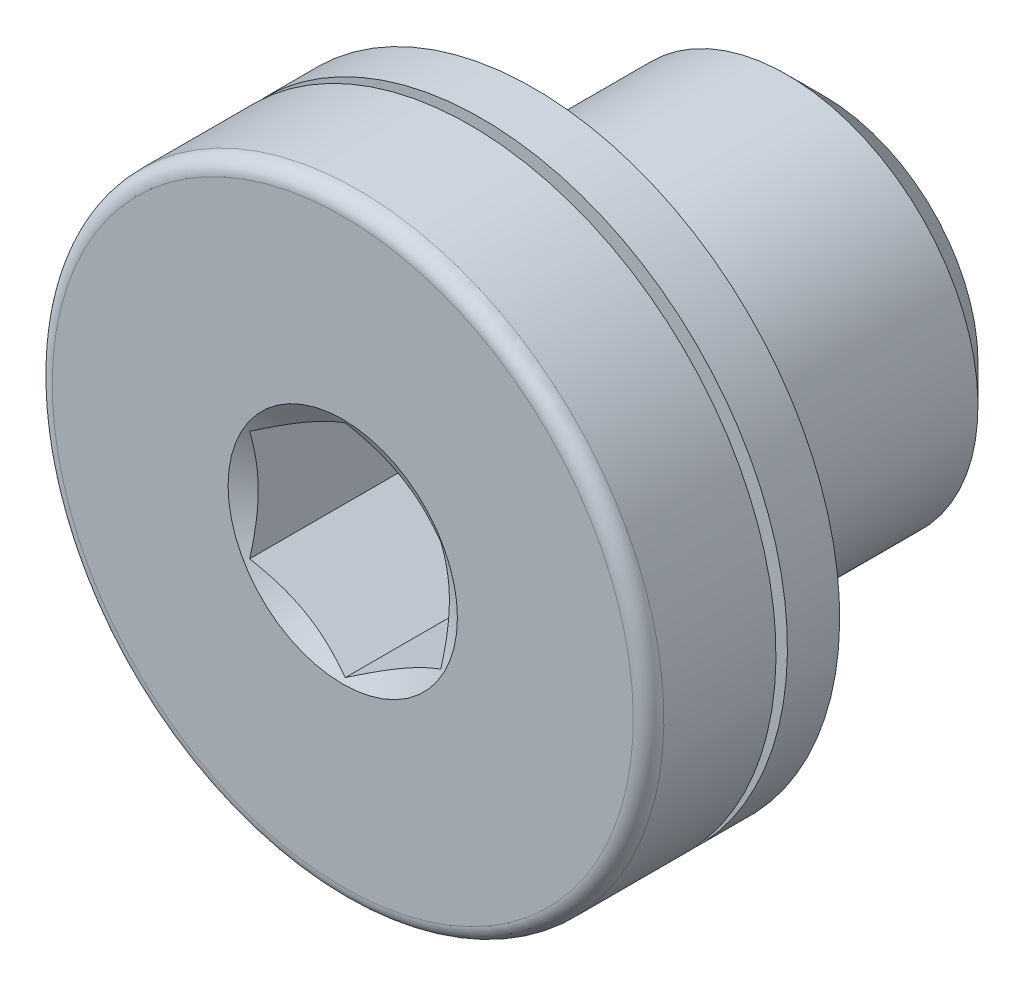
SolidWorks part; units mm, degrees
ref_plane "Front Plane" through (0, 0, 0) normal (0, 0, 1) x (1, 0, 0)
ref_plane "Top Plane" through (0, 0, 0) normal (0, 1, 0) x (1, 0, 0)
ref_plane "Right Plane" through (0, 0, 0) normal (1, 0, 0) x (0, 0, -1)
ref_plane "Plane1" through (0, 0, 0) normal (1, 0, 0) x (0, 0, -1)
sketch "Sketch1" plane through (0, 0, 0) normal (1, 0, 0) x (0, 0, -1)
  line L0 (-1.634, 0) -> (-2.5, 1.5)
  line L1 (-2.5, 1.5) -> (-2.5, 3.8)
  line L2 (-2.3, 4) -> (-0.8333, 4)
  line L3 (-0.8333, 4) -> (-0.8333, 3.6)
  line L4 (-0.8333, 3.6) -> (-0.6833, 3.6)
  line L5 (-0.6833, 3.6) -> (-0.6833, 4)
  line L6 (-0.6833, 4) -> (0, 4)
  line L7 (0, 4) -> (0, 2.0095)
  line L8 (0, 2.0095) -> (0.4905, 2.5)
  line L9 (0.4905, 2.5) -> (3.3095, 2.5)
  line L10 (3.3095, 2.5) -> (3.8, 2.0095)
  line L11 (3.8, 2.0095) -> (3.8, 0)
  line L12 (3.8, 0) -> (-1.634, 0)
  line L13 (3.8, 0) -> (-1.634, 0) construction
  arc A0 (-2.5, 3.8) -> (-2.3, 4) centre (-2.3, 3.8) cw
revolve "Revolve1" add sketch "Sketch1" angle 360 about L13
cosmetic thread "Cosmetic Thread1" parameters "D1"=3.8, "D2"=4.019
ref_plane "Plane2" through (0, 0, 2.5) normal (0, 0, 1) x (1, 0, 0)
sketch "Sketch2" plane through (0, 0, 2.5) normal (0, 0, 1) x (1, 0, 0)
  line L0 (-1.25, -0.7217) -> (0, -1.4434)
  line L1 (0, -1.4434) -> (1.25, -0.7217)
  line L2 (1.25, -0.7217) -> (1.25, 0.7217)
  line L3 (1.25, 0.7217) -> (0, 1.4434)
  line L4 (0, 1.4434) -> (-1.25, 0.7217)
  line L5 (-1.25, 0.7217) -> (-1.25, -0.7217)
extrude "Cut-Extrude1" cut sketch "Sketch2" against normal blind 2.5
